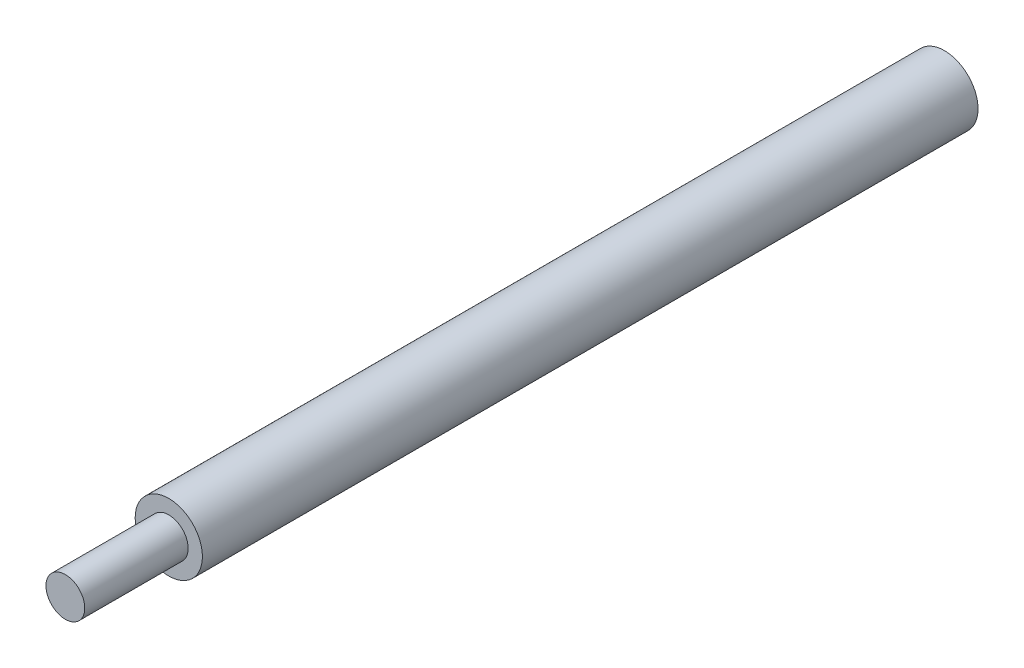
SolidWorks part; units mm, degrees
ref_plane "Front" through (0, 0, 0) normal (0, 0, 1) x (1, 0, 0)
ref_plane "Top" through (0, 0, 0) normal (0, 1, 0) x (1, 0, 0)
ref_plane "Right" through (0, 0, 0) normal (1, 0, 0) x (0, 0, -1)
sketch "草图1" plane through (0, 0, 0) normal (0, 0, 1) x (1, 0, 0)
  circle A0 centre (0, 0) radius 1.5
extrude "凸台-拉伸1" add sketch "草图1" along normal blind 8
sketch "草图2" plane through (0, 0, 0) normal (0, 0, -1) x (-1, 0, 0)
  circle A0 centre (0, 0) radius 2.6
extrude "凸台-拉伸2" add sketch "草图2" along normal blind 60
